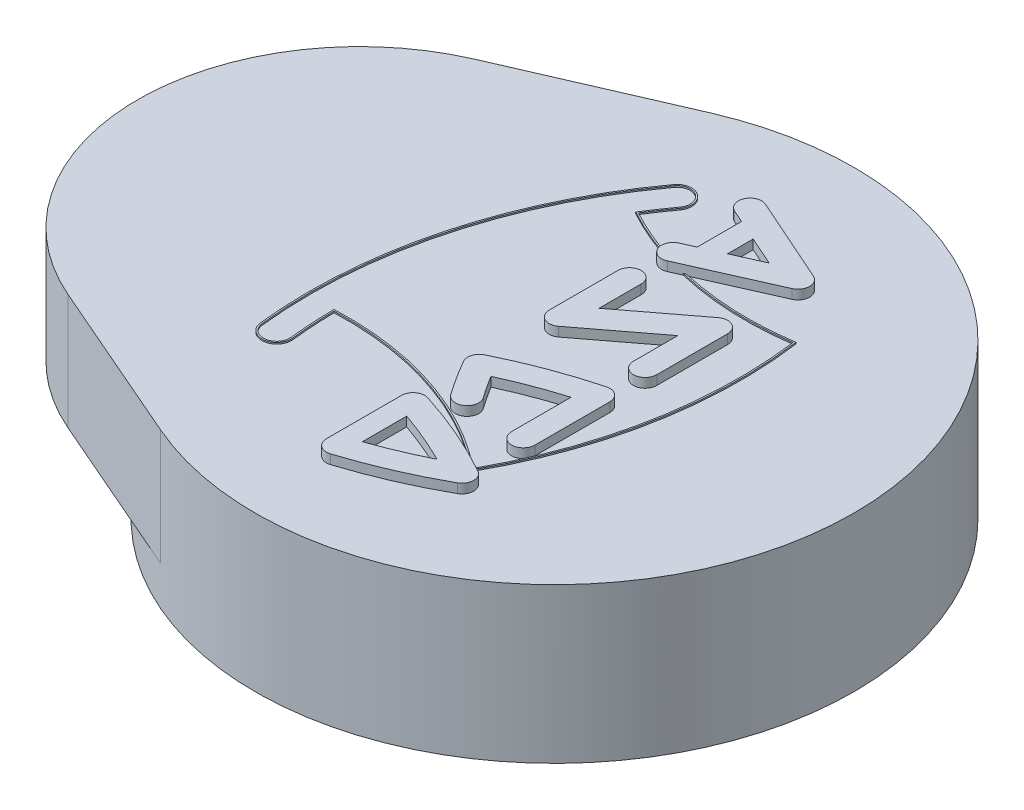
SolidWorks part; units mm, degrees
ref_plane "Front Plane" through (0, 0, 0) normal (0, 0, 1) x (1, 0, 0)
ref_plane "Top Plane" through (0, 0, 0) normal (0, 1, 0) x (1, 0, 0)
ref_plane "Right Plane" through (0, 0, 0) normal (1, 0, 0) x (0, 0, -1)
ref_plane "Plane1" through (0, 10.3836, 0) normal (0, -1, 0) x (-1, 0, 0)
sketch "Sketch1" plane through (0, 10.3836, 0) normal (0, -1, 0) x (-1, 0, 0)
  circle A0 centre (-86.1568, 0.1884) radius 6.5151
extrude "Boss-Extrude1" add sketch "Sketch1" along normal blind 3.3676
ref_plane "Plane2" through (0, 7.869, 0) normal (0, 1, 0) x (1, 0, 0)
sketch "Sketch2" plane through (0, 7.869, 0) normal (0, 1, 0) x (1, 0, 0)
  line L0 (83.5625, 6.1646) -> (79.9933, 4.6152)
  line L1 (79.9933, -4.2385) -> (83.5625, -5.7879)
  arc A0 (83.5625, -5.7879) -> (83.5625, 6.1646) centre (86.1568, 0.1884) ccw
  arc A1 (79.9933, 4.6152) -> (79.9933, -4.2385) centre (81.915, 0.1884) ccw
extrude "Boss-Extrude2" add sketch "Sketch2" along normal blind 2.5146
ref_plane "Plane3" through (0, 10.4154, 0) normal (0, 1, 0) x (1, 0, 0)
sketch "Sketch3" plane through (0, 10.4154, 0) normal (0, 1, 0) x (1, 0, 0)
  line L0 (86.3794, 2.8349) -> (86.3312, 2.8135)
  arc A0 (84.5517, 4.3863) -> (82.6631, -2.7176) centre (92.7252, -1.5896) ccw
  arc A1 (82.6631, -2.7176) -> (83.3005, -2.6461) centre (82.9818, -2.6818) ccw
  arc A2 (83.3005, -2.6461) -> (83.242, -1.6947) centre (92.7252, -1.5896) cw
  arc A3 (83.242, -1.6947) -> (87.6511, -3.1318) centre (83.5187, -8.3278) cw
  arc A4 (87.6511, -3.1318) -> (87.736, -3.1758) centre (82.9378, -12.3326) cw
  arc A5 (87.736, -3.1758) -> (88.8538, 2.7431) centre (79.4254, 1.4588) ccw
  arc A6 (88.8538, 2.7431) -> (86.3794, 2.8349) centre (87.8586, 9.307) cw
  arc A7 (86.3312, 2.8135) -> (88.8267, 2.7069) centre (87.8586, 9.307) ccw
  arc A8 (88.8267, 2.7069) -> (87.7172, -3.1442) centre (79.4254, 1.4588) cw
  arc A9 (87.7172, -3.1442) -> (83.21, -1.6643) centre (83.5187, -8.3278) ccw
  arc A10 (83.21, -1.6643) -> (83.2689, -2.6497) centre (92.7252, -1.5896) ccw
  arc A11 (83.2689, -2.6497) -> (82.6947, -2.714) centre (82.9818, -2.6818) cw
  arc A12 (82.6947, -2.714) -> (84.5774, 4.3676) centre (92.7252, -1.5896) cw
  arc A13 (84.5774, 4.3676) -> (85.0438, 4.0265) centre (84.8106, 4.197) cw
  arc A14 (85.0438, 4.0265) -> (84.6569, 3.4549) centre (92.7252, -1.5896) ccw
  arc A15 (84.6569, 3.4549) -> (85.7381, 2.9823) centre (87.8586, 9.307) ccw
  arc A16 (85.7381, 2.9823) -> (85.7455, 3.0133) centre (85.9885, 2.9391) cw
  arc A17 (85.7455, 3.0133) -> (84.7017, 3.4666) centre (87.8586, 9.307) cw
  arc A18 (84.7017, 3.4666) -> (85.0695, 4.0078) centre (92.7252, -1.5896) cw
  arc A19 (85.0695, 4.0078) -> (84.5517, 4.3863) centre (84.8106, 4.197) ccw
extrude "Boss-Extrude3" add sketch "Sketch3" against normal blind 0.0318
ref_plane "Plane4" through (0, 10.3836, 0) normal (0, 1, 0) x (1, 0, 0)
sketch "Sketch4" plane through (0, 10.3836, 0) normal (0, 1, 0) x (1, 0, 0)
  line L0 (87.9712, 4.0066) -> (86.0916, 4.842)
  line L1 (85.8853, 4.3778) -> (86.1568, 4.2571)
  line L2 (86.1568, 4.2571) -> (86.1568, 3.2919)
  line L3 (86.1568, 3.2919) -> (85.8853, 3.1713)
  line L4 (86.0916, 2.707) -> (87.9712, 3.5424)
  line L5 (87.2427, 3.7745) -> (86.614, 4.0539)
  line L6 (86.614, 4.0539) -> (86.614, 3.4951)
  line L7 (86.614, 3.4951) -> (87.2427, 3.7745)
  arc A0 (87.9712, 3.5424) -> (87.9712, 4.0066) centre (87.8681, 3.7745) ccw
  arc A1 (86.0916, 4.842) -> (85.8853, 4.3778) centre (85.9885, 4.6099) ccw
  arc A2 (85.8853, 3.1713) -> (86.0916, 2.707) centre (85.9885, 2.9391) ccw
extrude "Boss-Extrude4" add sketch "Sketch4" along normal blind 0.2032
ref_plane "Plane5" through (0, 10.3836, 0) normal (0, 1, 0) x (1, 0, 0)
sketch "Sketch5" plane through (0, 10.3836, 0) normal (0, 1, 0) x (1, 0, 0)
  line L0 (88.1221, 0.4473) -> (88.1221, 1.9887)
  line L1 (87.7143, 2.1909) -> (86.2425, 1.0712)
  line L2 (86.2425, 1.0712) -> (86.2425, 1.9887)
  line L3 (85.7345, 1.9887) -> (85.7345, 0.495)
  line L4 (86.1422, 0.2929) -> (87.6141, 1.4125)
  line L5 (87.6141, 1.4125) -> (87.6141, 0.4473)
  arc A0 (88.1221, 1.9887) -> (87.7143, 2.1909) centre (87.8681, 1.9887) ccw
  arc A1 (86.2425, 1.9887) -> (85.7345, 1.9887) centre (85.9885, 1.9887) ccw
  arc A2 (85.7345, 0.495) -> (86.1422, 0.2929) centre (85.9885, 0.495) ccw
  arc A3 (87.6141, 0.4473) -> (88.1221, 0.4473) centre (87.8681, 0.4473) ccw
extrude "Boss-Extrude5" add sketch "Sketch5" along normal blind 0.2032
ref_plane "Plane6" through (0, 10.3836, 0) normal (0, 1, 0) x (1, 0, 0)
sketch "Sketch6" plane through (0, 10.3836, 0) normal (0, 1, 0) x (1, 0, 0)
  line L0 (88.1221, -2.2035) -> (88.1221, -0.5736)
  line L1 (87.6141, -0.9094) -> (87.6141, -2.2035)
  arc A0 (88.1221, -0.5736) -> (87.803, -0.3281) centre (87.8681, -0.5736) ccw
  arc A1 (87.803, -0.3281) -> (85.8761, -1.0503) centre (90.4495, -10.3214) ccw
  arc A2 (85.8761, -1.0503) -> (85.7685, -1.4052) centre (85.9885, -1.2781) ccw
  arc A3 (85.7685, -1.4052) -> (86.2536, -2.1657) centre (94.7188, 3.7682) ccw
  arc A4 (86.2536, -2.1657) -> (86.6696, -1.8741) centre (86.4616, -2.0199) ccw
  arc A5 (86.6696, -1.8741) -> (86.3495, -1.3875) centre (94.7188, 3.7682) cw
  arc A6 (86.3495, -1.3875) -> (87.6141, -0.9094) centre (90.4495, -10.3214) cw
  arc A7 (87.6141, -2.2035) -> (88.1221, -2.2035) centre (87.8681, -2.2035) ccw
extrude "Boss-Extrude6" add sketch "Sketch6" along normal blind 0.2032
ref_plane "Plane7" through (0, 10.3836, 0) normal (0, 1, 0) x (1, 0, 0)
sketch "Sketch7" plane through (0, 10.3836, 0) normal (0, 1, 0) x (1, 0, 0)
  line L0 (85.7345, -2.7213) -> (85.7345, -4.3512)
  line L1 (86.1822, -3.0537) -> (86.1822, -4.0189)
  arc A0 (87.9922, -3.7578) -> (87.9922, -3.3147) centre (87.8681, -3.5363) ccw
  arc A1 (87.9922, -3.3147) -> (86.0653, -2.4792) centre (82.9378, -12.3326) ccw
  arc A2 (86.0653, -2.4792) -> (85.7345, -2.7213) centre (85.9885, -2.7213) ccw
  arc A3 (85.7345, -4.3512) -> (86.0653, -4.5933) centre (85.9885, -4.3512) ccw
  arc A4 (86.0653, -4.5933) -> (87.9922, -3.7578) centre (82.9378, 5.2601) ccw
  arc A5 (87.3252, -3.5363) -> (86.1822, -3.0537) centre (82.9378, -12.3326) ccw
  arc A6 (86.1822, -4.0189) -> (87.3252, -3.5363) centre (82.9378, 5.2601) ccw
extrude "Boss-Extrude7" add sketch "Sketch7" along normal blind 0.2032
